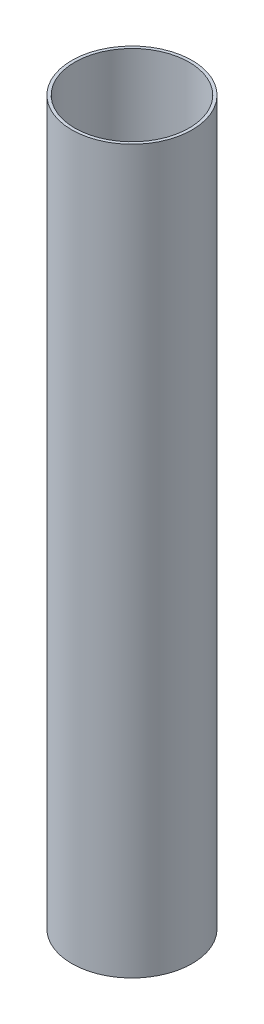
SolidWorks part; units mm, degrees
material "6061-T6 (SS)"
ref_plane "Front Plane" through (0, 0, 0) normal (0, 0, 1) x (1, 0, 0)
ref_plane "Top Plane" through (0, 0, 0) normal (0, 1, 0) x (1, 0, 0)
ref_plane "Right Plane" through (0, 0, 0) normal (1, 0, 0) x (0, 0, -1)
ref_axis "Axis1" through (0, 819.187, 0) along (0, -1, 0)
sketch "Sketch2" plane through (0, 0, 0) normal (0, 0, 1) x (1, 0, 0)
  line L0 (-63.5, 0) -> (-63.5, 762)
  line L1 (-60.325, 0) -> (-63.5, 0)
  line L2 (-60.325, 0) -> (-60.325, 762)
  line L4 (-63.5, 381) -> (-59.436, 381) construction
  line L5 (0, 819.187) -> (0, -55) construction
  line L6 (-60.325, 762) -> (-63.5, 762)
  line L13 (55, 0) -> (-55, 0) construction
  point P0 (-60.4607, 0)
  point P1 (-63.5, 381)
  point P17 (-60.325, 381)
  dimension "D2" = 3.175
  dimension "D3" = 381
  dimension "D4" = 63.5
revolve "Revolve1" add sketch "Sketch2" angle 360 about axis through (0, 819.187, 0) along (0, -1, 0)
